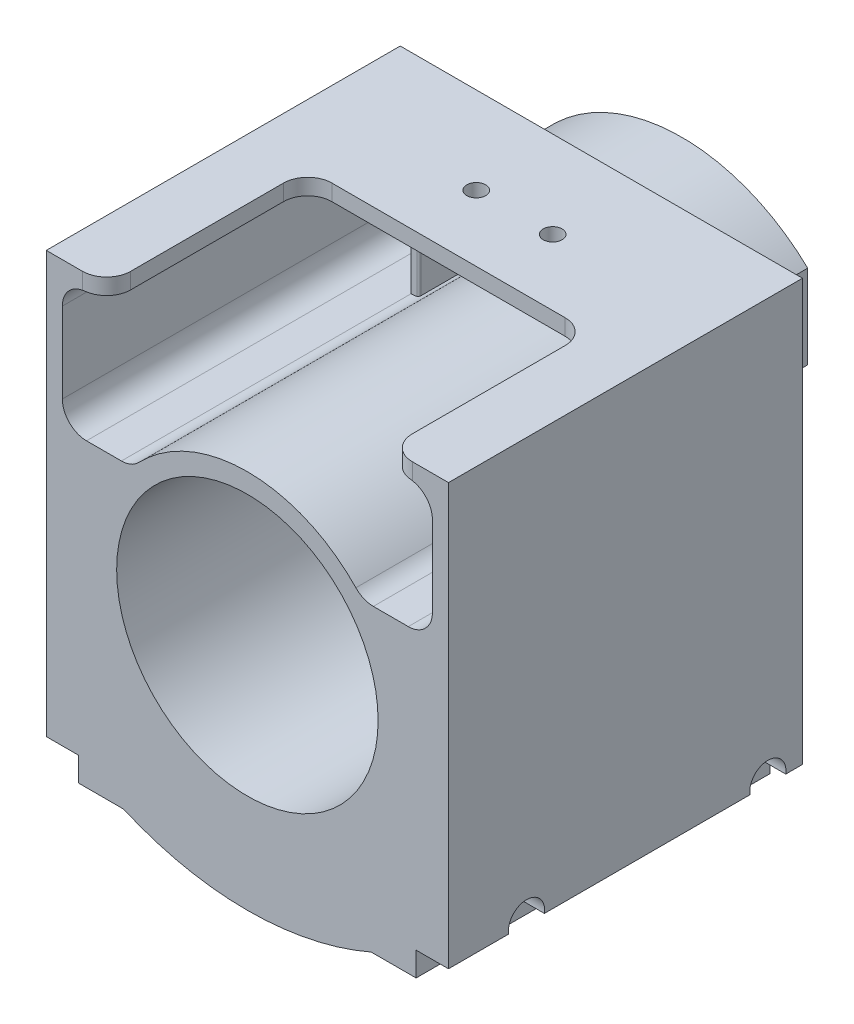
SolidWorks part; units mm, degrees
ref_plane "Front Plane" through (0, 0, 0) normal (0, 0, 1) x (1, 0, 0)
ref_plane "Top Plane" through (0, 0, 0) normal (0, 1, 0) x (1, 0, 0)
ref_plane "Right Plane" through (0, 0, 0) normal (1, 0, 0) x (0, 0, -1)
sketch "Sketch1" plane through (0, 0, 0) normal (0, 0, 1) x (1, 0, 0)
  line L1 (0, 0) -> (0, -38.55) construction
  line L2 (-25, 0) -> (-25, -29.3445)
  line L3 (25, 0) -> (25, -29.3445)
  line L4 (-25, 0) -> (-25, 20)
  line L5 (-25, 20) -> (25, 20)
  line L6 (25, 20) -> (25, 0)
  line L7 (25, -29.3445) -> (25, -32.3445)
  line L8 (25, -32.3445) -> (20.9746, -32.3445)
  line L9 (20.9746, -32.3445) -> (20.9746, -35.3445)
  line L10 (20.9746, -35.3445) -> (15.3904, -35.3445)
  line L11 (-20.9746, -35.3445) -> (-15.3904, -35.3445)
  line L12 (-20.9746, -32.3445) -> (-20.9746, -35.3445)
  line L13 (-25, -32.3445) -> (-20.9746, -32.3445)
  line L14 (-25, -29.3445) -> (-25, -32.3445)
  arc A0 (-25, -29.3445) -> (-20.9746, -32.3445) centre (0, 0) ccw construction
  arc A1 (20.9746, -32.3445) -> (25, -29.3445) centre (0, 0) ccw construction
  arc A2 (15.3904, -35.3445) -> (20.9746, -32.3445) centre (0, 0) ccw construction
  arc A3 (-15.3904, -35.3445) -> (15.3904, -35.3445) centre (0, 0) ccw
  arc A4 (-20.9746, -32.3445) -> (-15.3904, -35.3445) centre (0, 0) ccw construction
  dimension "D1" = 77.1
  dimension "D2" = 50
  dimension "D3" = 20
  dimension "D4" = 3
  dimension "D5" = 3
extrude "Boss-Extrude2" add sketch "Sketch1" along normal blind 44 from offset 6
sketch "Sketch2" plane through (0, 0, 50) normal (0, 0, 1) x (1, 0, 0)
  line L6 (0, 6.25) -> (0, -26.25) construction
  circle A0 centre (0, -10) radius 16.25
  dimension "D2" = 32.5
  dimension "D1" = 10
extrude "Cut-Extrude1" cut sketch "Sketch2" against normal through all both
sketch "Sketch4" plane through (0, 0, 50) normal (0, 0, 1) x (1, 0, 0)
  line L0 (-23, 18) -> (23, 18)
  line L3 (0, 20) -> (0, 6.25) construction
  line L4 (25, 20) -> (-25, 20) construction
  line L5 (23, 2) -> (14.3178, 2)
  line L6 (-23, 18) -> (-23, 2)
  line L7 (-23, 2) -> (-14.3178, 2)
  line L8 (-25, 20) -> (-25, -32.3445) construction
  line L9 (23, 18) -> (23, 2)
  circle A2 centre (0, -10) radius 16.25 construction
  arc A3 (14.3178, 2) -> (-14.3178, 2) centre (0, -10) ccw
  point P2 (0, 13.125)
  point P14 (0, 18)
  dimension "D1" = 37.3631
  dimension "D2" = 2
  dimension "D3" = 2
  dimension "D4" = 16
extrude "Cut-Extrude3" cut sketch "Sketch4" against normal through all
fillet "Fillet1" radius 3 6 edges at (23, 18, 28) (23, 2, 28) (14.3178, 2, 28) (-14.3178, 2, 28) (-23, 2, 28) (-23, 18, 28)
sketch "Sketch5" plane through (0, 20, 0) normal (0, 1, 0) x (1, 0, 0)
  line L0 (25, -50) -> (-25, -50) construction
  line L1 (-17.5, -50) -> (17.5, -50)
  line L2 (-17.5, -50) -> (-17.5, -25)
  line L3 (-17.5, -25) -> (17.5, -25)
  line L4 (17.5, -50) -> (17.5, -25)
  line L5 (0, 0) -> (0, -50) construction
  dimension "D1" = 35
  dimension "D2" = 25
extrude "Cut-Extrude4" cut sketch "Sketch5" against normal blind 10
fillet "Fillet2" radius 3 4 edges at (17.5, 19, 50) (17.5, 19, 25) (-17.5, 19, 25) (-17.5, 19, 50)
ref_plane "Plane1" through (0, 0, 14) normal (0, 0, 1) x (1, 0, 0)
sketch "Sketch6" plane through (0, 0, 14) normal (0, 0, 1) x (1, 0, 0)
  line L0 (0, -10) -> (0, 3) construction
  line L1 (0, -10) -> (4.4463, 2.216) construction
  circle A1 centre (0, -10) radius 16.25 construction
  circle A3 centre (0, -10) radius 9.5
  circle A8 centre (0, -10) radius 16.25
  circle A9 centre (0, -10) radius 13 construction
  circle A10 centre (4.4463, 2.216) radius 1.65
  circle A11 centre (12.216, -14.4463) radius 1.65
  circle A12 centre (-4.4463, -22.216) radius 1.65
  circle A13 centre (-12.216, -5.5537) radius 1.65
  dimension "D1" = 19
  dimension "D6" = 13
  dimension "D2" = 3.5
  dimension "D3" = 3.3
  dimension "D4" = 20
  dimension "D5" = 4
extrude "Boss-Extrude3" add sketch "Sketch6" against normal blind 5
sketch "Sketch7" plane through (0, 0, 0) normal (1, 0, 0) x (0, 0, -1)
  circle A0 centre (-40.3, -32) radius 2.25
  circle A1 centre (-10.3, -32) radius 2.25
  dimension "D3" = 4.5
  dimension "D1" = 32
  dimension "D2" = 10.3
  dimension "D4" = 30
extrude "Cut-Extrude5" cut sketch "Sketch7" against normal through all both and the other way through all
sketch "Sketch8" plane through (0, 20, 0) normal (0, 1, 0) x (1, 0, 0)
  line L0 (0, -6) -> (0, -25) construction
  line L1 (25, -6) -> (-25, -6) construction
  line L2 (14.5, -25) -> (-14.5, -25) construction
  circle A0 centre (-4.75, -16.8) radius 1.175
  circle A1 centre (4.75, -16.8) radius 1.175
  dimension "D1" = 2.35
  dimension "D2" = 9.5
  dimension "D3" = 10.8
extrude "Cut-Extrude6" cut sketch "Sketch8" against normal up to next contours A0 | A1
sketch "Sketch9" plane through (0, 0, 50) normal (0, 0, 1) x (1, 0, 0)
  line L0 (0, -28.5) -> (0, -5) construction
  line L1 (0, -10) -> (0, -28.5) construction
  line L2 (-15.6553, 2) -> (-15.6553, 11.4123)
  line L3 (15.6553, 2) -> (15.6553, 11.4123)
  line L4 (0, 8.6815) -> (0, 17.6815) construction
  line L5 (-14.6553, 2.1716) -> (-14.6553, 10.5325)
  line L6 (14.6553, 2.1716) -> (14.6553, 10.5325)
  line L7 (-15.6553, 2) -> (-15.6553, 1)
  line L8 (15.6553, 2) -> (15.6553, 1)
  line L9 (14.6553, 2) -> (14.6553, 10.9784) construction
  line L10 (-14.6553, 2) -> (-14.6553, 10.9784) construction
  arc A0 (13.4892, 2.9245) -> (-13.4892, 2.9245) centre (0, -10) ccw construction
  arc A1 (13.4892, 2.9245) -> (-13.4892, 2.9245) centre (0, -10) ccw
  arc A3 (-15.6553, 11.4123) -> (15.6553, 11.4123) centre (0, -5) cw
  arc A4 (13.4892, 2.9245) -> (15.6553, 2) centre (15.6553, 5) ccw construction
  arc A5 (-15.6553, 2) -> (-13.4892, 2.9245) centre (-15.6553, 5) ccw construction
  arc A6 (13.4892, 2.9245) -> (15.6553, 2) centre (15.6553, 5) ccw
  arc A7 (-15.6553, 2) -> (-13.4892, 2.9245) centre (-15.6553, 5) ccw
  arc A8 (12.7671, 2.2327) -> (15.6553, 1) centre (15.6553, 5) ccw
  arc A9 (12.7671, 2.2327) -> (-12.7671, 2.2327) centre (0, -10) ccw
  arc A10 (-15.6553, 1) -> (-12.7671, 2.2327) centre (-15.6553, 5) ccw
  arc A11 (-14.3156, 11.2835) -> (14.3156, 11.2835) centre (0, -5) cw
  arc A12 (-14.6553, 10.9784) -> (14.6553, 10.9784) centre (0, -5) cw construction
  arc A13 (14.6553, 10.5325) -> (14.3156, 11.2835) centre (13.6553, 10.5325) ccw
  arc A14 (-14.6553, 10.5325) -> (-14.3156, 11.2835) centre (-13.6553, 10.5325) cw
  dimension "D1" = 9
  dimension "D2" = 1
  dimension "D4" = 1
  dimension "Ring Gear Outer Dia to Center" = 23.5
  dimension "Pinion to Ring Gear Outer Diameter" = 18.5
  dimension "D3" = 1
extrude "Boss-Extrude4" add sketch "Sketch9" along normal blind 8 and the other way blind 10 from surface at -44 contours L5 A11 L6 L2 L3 A3 A6 | L7 A10 A9 A8 L8 L2 L3 A6
fillet "Fillet5" radius 0.25 8 edges at (14.0281, 2.4797, -4) (-14.0281, 2.4797, -4) (14.6553, 6.352, -4) (14.5664, 10.9446, -4) (-14.6553, 6.352, -4) (-14.5664, 10.9446, -4) (0, 8.6815, -4) (0, 16.6815, -4)
fillet "Fillet6" radius 0.25 5 edges at (14.6553, 6.352, 14) (14.5664, 10.9446, 14) (-14.6553, 6.352, 14) (-14.5664, 10.9446, 14) (0, 16.6815, 14)
